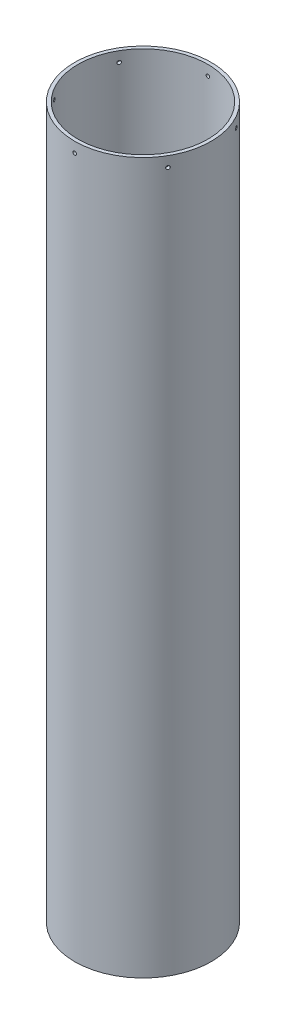
SolidWorks part; units mm, degrees
ref_plane "Front Plane" through (0, 0, 0) normal (0, 0, 1) x (1, 0, 0)
ref_plane "Top Plane" through (0, 0, 0) normal (0, 1, 0) x (1, 0, 0)
ref_plane "Right Plane" through (0, 0, 0) normal (1, 0, 0) x (0, 0, -1)
sketch "Sketch1" plane through (0, 0, 0) normal (0, 1, 0) x (1, 0, 0)
  circle A0 centre (0, 0) radius 63.5
  circle A1 centre (0, 0) radius 60.325
  dimension "D1" = 127
  dimension "D2" = 3.175
extrude "Boss-Extrude1" add sketch "Sketch1" along normal blind 660.4
hole_wizard "#4 Clearance Hole2" positions "Sketch2" profile "Sketch4" hole size "#4" standard "ANSI Inch"
sketch "Sketch2" plane through (0, 0, 0) normal (0, 0, 1) x (1, 0, 0)
  line L0 (60.325, 660.4) -> (-60.325, 660.4) construction
  point P0 (0, 650.875)
  dimension "D1" = 9.525
sketch "Sketch4" plane through (0, 650.875, 0) normal (1, 0, 0) x (0, 1, 0)
  line L0 (0, 0) -> (0, 63.5)
  line L1 (0, 63.5) -> (1.6319, 63.5)
  line L2 (1.6319, 63.5) -> (1.6319, 0)
  line L5 (1.6319, 0) -> (0, 0)
  line L11 (0, -6.35) -> (0, 107.95) construction
  dimension "Thru Hole Dia." = 3.2639
  dimension "Thru Hole Depth" = 63.5
pattern_circular "CirPattern1" count 6 over 360 about axis through (0, 660.4, 0) along (0, 1, 0) of "#4 Clearance Hole2"
